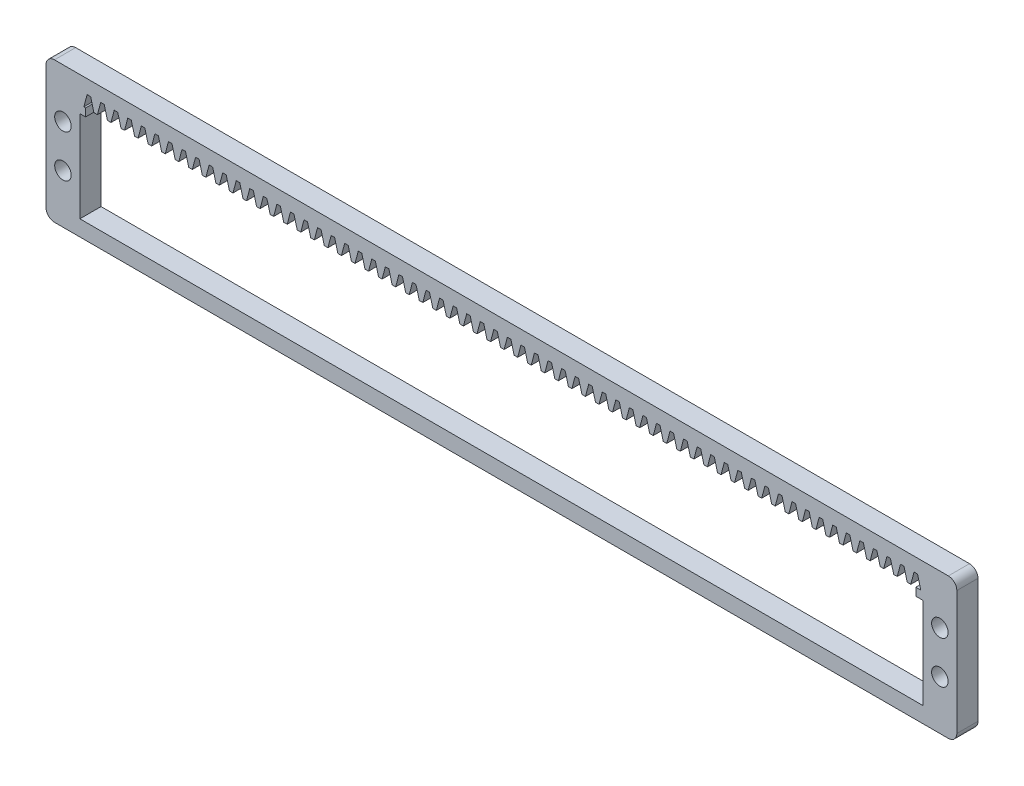
SolidWorks part; units mm, degrees
other "Markup1"
sketch "Sketch6" plane through (0, -30, 3.6) normal (0, 0, 1) x (1, 0, 0)
other "Markup2"
sketch "Sketch7" plane through (0, -30, 3.6) normal (0, 0, 1) x (1, 0, 0)
ref_plane "Front Plane" through (0, 0, 0) normal (0, 0, 1) x (1, 0, 0)
ref_plane "Top Plane" through (0, 0, 0) normal (0, 1, 0) x (1, 0, 0)
ref_plane "Right Plane" through (0, 0, 0) normal (1, 0, 0) x (0, 0, -1)
sketch "Sketch1" plane through (0, 0, 0) normal (0, 0, 1) x (1, 0, 0)
  line L1 (2, 0) -> (213, 0)
  line L2 (0, -2) -> (0, -31.22)
  line L3 (2, -33.22) -> (213, -33.22)
  line L4 (215, -2) -> (215, -31.22)
  arc A0 (213, -33.22) -> (215, -31.22) centre (213, -31.22) ccw
  arc A1 (0, -31.22) -> (2, -33.22) centre (2, -31.22) ccw
  arc A2 (2, 0) -> (0, -2) centre (2, -2) ccw
  arc A3 (213, 0) -> (215, -2) centre (213, -2) cw
  point P7 (215, -33.22)
  point P12 (0, 0)
  point P15 (215, 0)
  dimension "D3" = 2
  dimension "D1" = 33.22
  dimension "D2" = 215
extrude "Boss-Extrude1" add sketch "Sketch1" along normal blind 5
sketch "Sketch2" plane through (0, 0, 5) normal (0, 0, 1) x (1, 0, 0)
  line L0 (2, -33.22) -> (213, -33.22) construction
  line L1 (8, -8) -> (207, -8)
  line L2 (8, -8) -> (8, -29.5)
  line L3 (8, -29.5) -> (207, -29.5)
  line L4 (207, -8) -> (207, -29.5)
  line L5 (0, -2) -> (0, -31.22) construction
  line L7 (215, -31.22) -> (215, -2) construction
  line L8 (8, -18.75) -> (207, -18.75) construction
  line L12 (8, -29.5) -> (207, -29.5) construction
  line L13 (207, -4.3144) -> (207, -29.5) construction
  dimension "D1" = 21.5
  dimension "D2" = 8
  dimension "D3" = 8
  dimension "D4" = 3.72
extrude "Cut-Extrude1" cut sketch "Sketch2" against normal through all
sketch "Sketch3" plane through (0, 0, 5) normal (0, 0, 1) x (1, 0, 0)
  line L0 (207, -8) -> (8, -8) construction
  line L1 (9.35, -8) -> (205.32, -8)
  line L2 (9.35, -8) -> (9.35, -6.15)
  line L3 (9.35, -6.15) -> (205.32, -6.15)
  line L4 (205.32, -8) -> (205.32, -6.15)
  line L5 (207, -29.5) -> (207, -8) construction
  line L6 (8, -8) -> (8, -29.5) construction
  dimension "D1" = 1.85
  dimension "D2" = 1.68
  dimension "D3" = 1.35
extrude "Cut-Extrude2" cut sketch "Sketch3" against normal through all
sketch "Sketch4" plane through (0, 0, 5) normal (0, 0, 1) x (1, 0, 0)
  line L0 (207.7, -6.15) -> (206.5, -6.15) construction
  line L1 (205.32, -6.15) -> (9.35, -6.15) construction
  line L2 (207.7, -6.15) -> (208.465, -3.2492) construction
  line L3 (208.465, -3.2492) -> (205.735, -3.2492) construction
  line L4 (205.735, -3.2492) -> (206.5, -6.15)
  line L5 (205.735, -3.2492) -> (204.905, -3.2492)
  line L6 (204.905, -3.2492) -> (204.14, -6.15)
  line L7 (204.14, -6.15) -> (206.5, -6.15)
  line L10 (206.5, -6.15) -> (207.7, -6.15) construction
  dimension "D1" = 1.2
  dimension "D3" = 3
  dimension "D4" = 0.83
  dimension "D5" = 2.73
extrude "Cut-Extrude4" cut sketch "Sketch4" against normal through all
pattern_linear "LPattern1" count 62 spacing 3.2 along (-1, 0, 0) of "Cut-Extrude4"
sketch "Sketch5" plane through (0, 0, 5) normal (0, 0, 1) x (1, 0, 0)
  line L0 (207, -16.61) -> (215, -16.61) construction
  line L1 (213, 0) -> (2, 0) construction
  line L2 (8, -8) -> (8, -29.5) construction
  line L3 (0, -2) -> (0, -31.22) construction
  line L4 (2, -33.22) -> (213, -33.22) construction
  line L5 (0, -16.61) -> (8, -16.61) construction
  line L7 (211, -11.61) -> (211, -21.61) construction
  line L8 (4, -11.61) -> (4, -21.61) construction
  line L9 (207, -29.5) -> (207, -8) construction
  line L10 (215, -31.22) -> (215, -2) construction
  circle A4 centre (4, -11.61) radius 1.95
  circle A5 centre (4, -21.61) radius 1.95
  circle A6 centre (211, -11.61) radius 1.95
  circle A7 centre (211, -21.61) radius 1.95
  point P8 (211, -16.61)
  point P18 (4, -16.61)
  point P22 (4, -16.61)
  point P31 (211, -16.61)
  dimension "D1" = 3.9
  dimension "D3" = 3.9
  dimension "D4" = 3.9
  dimension "D6" = 3.9
  dimension "D5" = 10
  dimension "D7" = 10
extrude "Cut-Extrude5" cut sketch "Sketch5" against normal blind 10
